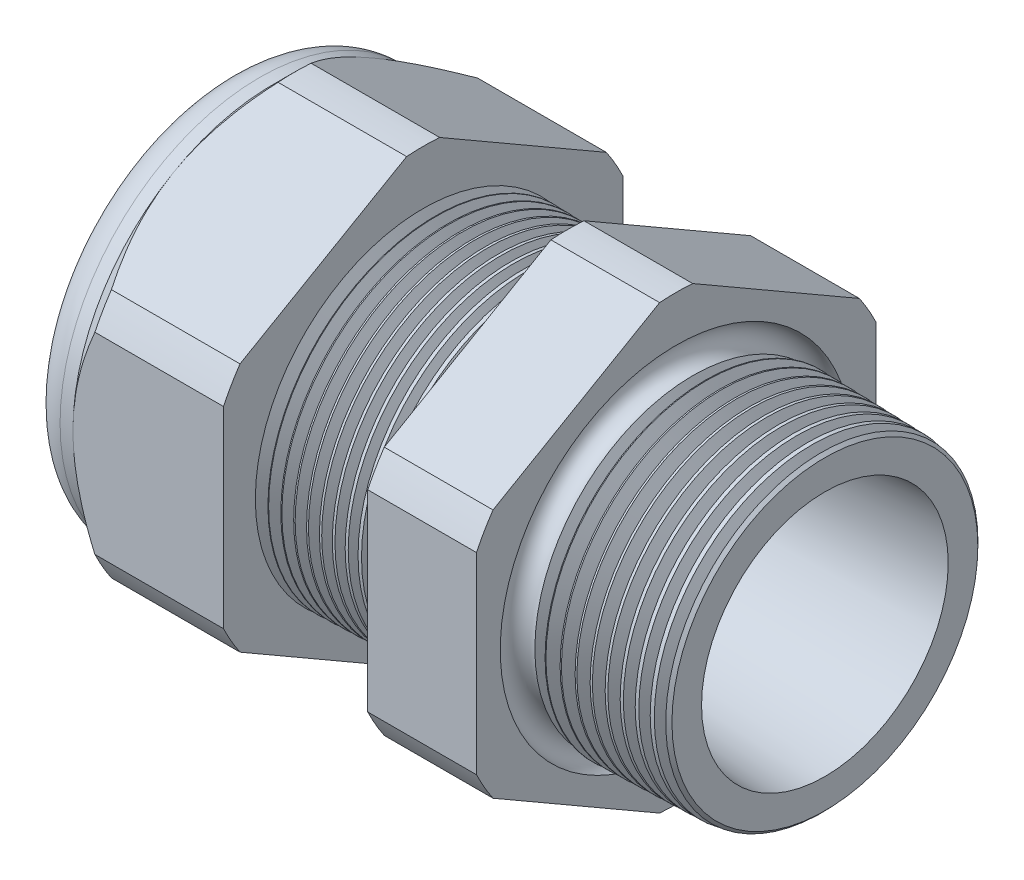
SolidWorks part; units mm, degrees
ref_plane "Front Plane" through (0, 0, 0) normal (0, 0, 1) x (1, 0, 0)
ref_plane "Top Plane" through (0, 0, 0) normal (0, 1, 0) x (1, 0, 0)
ref_plane "Right Plane" through (0, 0, 0) normal (1, 0, 0) x (0, 0, -1)
sketch "Sketch10" plane through (0, 0, 0) normal (0, 0, 1) x (1, 0, 0)
  line L0 (0, 0) -> (-115.3565, 0) construction
  line L1 (-34.798, 5.969) -> (-22.998, 5.969)
  line L2 (1.016, 7.3722) -> (1.016, 9.4042)
  line L3 (-7.874, 9.637) -> (1.016, 9.4042)
  line L4 (-7.874, 23.876) -> (-7.874, 9.637)
  line L5 (-7.874, 23.876) -> (-14.374, 23.876)
  line L6 (-14.374, 23.876) -> (-14.374, 9.8072)
  line L7 (-22.998, 10.033) -> (-14.374, 9.8072)
  line L8 (-22.998, 10.033) -> (-22.998, 23.876)
  line L9 (-22.998, 23.876) -> (-31.998, 23.876)
  line L10 (-31.998, 23.876) -> (-31.998, 11.938)
  line L11 (-31.998, 11.938) -> (-34.798, 11.938)
  line L12 (-34.798, 11.938) -> (-34.798, 5.969)
  line L13 (-22.998, 5.969) -> (1.016, 7.3722)
  dimension "D1" = 35.814
  dimension "D2" = 11.938
  dimension "D3" = 1.5
  dimension "D4" = 2.032
  dimension "A" = 20.066
  dimension "D6" = 23.876
  dimension "D8" = 47.752
  dimension "D9" = 2.8
  dimension "D10" = 9
  dimension "D11" = 6.5
  dimension "D" = 8.89
revolve "Revolve2" add sketch "Sketch10" angle 360 about L0
sketch "Sketch12" plane through (-31.998, 0, 0) normal (-1, 0, 0) x (0, 0, 1)
  line L1 (-0.9882, 13.2143) -> (-10.9498, 7.4629)
  line L2 (-11.938, 5.7513) -> (-11.938, -5.7513)
  line L3 (-10.9498, -7.4629) -> (-0.9882, -13.2143)
  line L4 (0.9882, -13.2143) -> (10.9498, -7.4629)
  line L5 (11.938, -5.7513) -> (11.938, 5.7513)
  line L6 (10.9498, 7.4629) -> (0.9882, 13.2143)
  circle A0 centre (0, 0) radius 11.938 construction
  arc A1 (0.9882, 13.2143) -> (-0.9882, 13.2143) centre (0, 0) ccw
  arc A2 (-10.9498, 7.4629) -> (-11.938, 5.7513) centre (0, 0) ccw
  arc A3 (-11.938, -5.7513) -> (-10.9498, -7.4629) centre (0, 0) ccw
  arc A4 (-0.9882, -13.2143) -> (0.9882, -13.2143) centre (0, 0) ccw
  arc A5 (10.9498, -7.4629) -> (11.938, -5.7513) centre (0, 0) ccw
  arc A6 (11.938, 5.7513) -> (10.9498, 7.4629) centre (0, 0) ccw
  dimension "D2" = 26.5024
  dimension "D1" = 23.876
extrude "Cut-Extrude2" cut sketch "Sketch12" against normal through all flip side to cut
fillet "Fillet4" radius 2.032 1 edges at (-34.798, 0, -11.938)
sketch "Sketch19" plane through (-31.998, 0, 0) normal (-1, 0, 0) x (0, 0, 1)
  line L0 (11.938, 0) -> (11.938, 5.7513) construction
  circle A0 centre (0, 0) radius 11.938
extrude "Cut-Extrude3" cut sketch "Sketch19" against normal blind 2 draft 45 flip side to cut
chamfer "Chamfer1" distance 0.254 angle 45 1 edges at (1.016, 0, -9.4042)
sketch "Sketch21" plane through (-34.798, 0, 0) normal (-1, 0, 0) x (0, 0, 1)
  circle A0 centre (0, 0) radius 5.969
  circle A2 centre (0, 0) radius 5.969 construction
extrude "plug" add sketch "Sketch21" against normal blind 6.35 separate body
sketch "Sketch22" plane through (-34.798, 0, 0) normal (-1, 0, 0) x (0, 0, 1)
  circle A0 centre (0, 0) radius 5.715
  circle A1 centre (0, 0) radius 5.969 construction
  dimension "D1" = 0.254
extrude "Cut-Extrude4" cut sketch "Sketch22" against normal blind 0.508
sketch "Sketch27" plane through (-34.29, 0, 0) normal (-1, 0, 0) x (0, 0, 1)
  line L0 (-4.3624, 0) -> (4.3624, 0) construction
  circle A0 centre (-3.5474, 0) radius 2.159
  circle A1 centre (0, 0) radius 5.715 construction
  dimension "D1" = 0.0086
  dimension "holedia" = 4.318
extrude "plugholes" cut sketch "Sketch27" against normal through all
pattern_circular "CirPattern1" count 2 over 360 about axis through (0, 0, 0) along (1, 0, 0) of "plugholes"
sketch "Sketch28" [suppressed] plane through (-29.464, 0, 0) normal (-1, 0, 0) x (0, 0, 1)
  circle A0 centre (0, 0) radius 0.762
  dimension "midholedia" = 4.318
extrude "midhole" [suppressed] cut sketch "Sketch28" against normal through all
sketch "Sketch29" plane through (0, 0, 0) normal (0, 0, 1) x (1, 0, 0)
  line L0 (-22.998, 10.033) -> (-22.265, 10.0138)
  line L1 (-14.374, 9.8072) -> (-22.998, 10.033) construction
  line L2 (-22.265, 10.0138) -> (-22.6481, 9.3886)
  line L3 (-22.6481, 9.3886) -> (-22.998, 10.033)
  dimension "D1" = 60
  dimension "D2" = 60
  dimension "D3" = 0.635
revolve "Cut-Revolve1" cut sketch "Sketch29" angle 360 about axis through (0, 0, 0) along (-1, 0, 0)
pattern_linear "LPattern1" count 11 spacing 0.762 along (1, 0, 0) of "Cut-Revolve1"
sketch "Sketch30" plane through (0, 0, 0) normal (0, 0, 1) x (1, 0, 0)
  line L0 (-7.874, 9.637) -> (-6.9944, 9.6139)
  line L1 (-7.874, 13.2143) -> (-7.874, 7.4629) construction
  line L2 (0.7621, 9.4108) -> (-7.874, 9.637) construction
  line L3 (-6.9944, 9.6139) -> (-7.4542, 8.8637)
  line L4 (-7.4542, 8.8637) -> (-7.874, 9.637)
  dimension "D1" = 60
  dimension "D2" = 60
  dimension "D3" = 0.762
revolve "Cut-Revolve2" cut sketch "Sketch30" angle 360 about axis through (0, 0, 0) along (-1, 0, 0)
pattern_linear "LPattern2" count 10 spacing 0.889 along (1, 0, 0) of "Cut-Revolve2"
sketch "Sketch31" [suppressed] plane through (-38.354, 0, 0) normal (-1, 0, 0) x (0, 0, 1)
  line L0 (-1.905, 1.905) -> (1.905, 1.905)
  line L1 (-1.905, -1.905) -> (1.905, -1.905)
  circle A0 centre (0, 0) radius 1.905 construction
  arc A1 (-1.905, 1.905) -> (-1.905, -1.905) centre (-1.905, 0) ccw
  arc A2 (1.905, 1.905) -> (1.905, -1.905) centre (1.905, 0) cw
extrude "Cut-Extrude5" [suppressed] cut sketch "Sketch31" against normal through all
sketch "Sketch32" plane through (0, 0, 0) normal (0, 0, 1) x (1, 0, 0)
  line L0 (-7.874, 13.2143) -> (-7.874, 7.4629) construction
  circle A0 centre (-7.747, 9.637) radius 0.889
  dimension "D2" = 1.778
  dimension "D1" = 0.127
revolve "Cut-Revolve3" cut sketch "Sketch32" angle 360 about axis through (0, 0, 0) along (-1, 0, 0)
